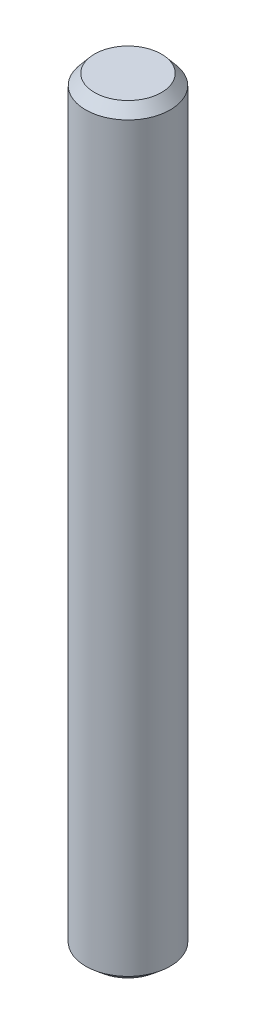
SolidWorks part; units mm, degrees
ref_plane "Plan de face" through (0, 0, 0) normal (0, 0, 1) x (1, 0, 0)
ref_plane "Plan de dessus" through (0, 0, 0) normal (0, 1, 0) x (1, 0, 0)
ref_plane "Plan de droite" through (0, 0, 0) normal (1, 0, 0) x (0, 0, -1)
sketch "Esquisse1" plane through (0, 0, 0) normal (0, 1, 0) x (1, 0, 0)
  circle A0 centre (0, 0) radius 4
  dimension "D1" = 8
extrude "Boss.-Extru.1" add sketch "Esquisse1" along normal blind 72
chamfer "Chanfrein1" distance 1 angle 40 2 edges at (0, 0, 4) (0, 72, 4)
